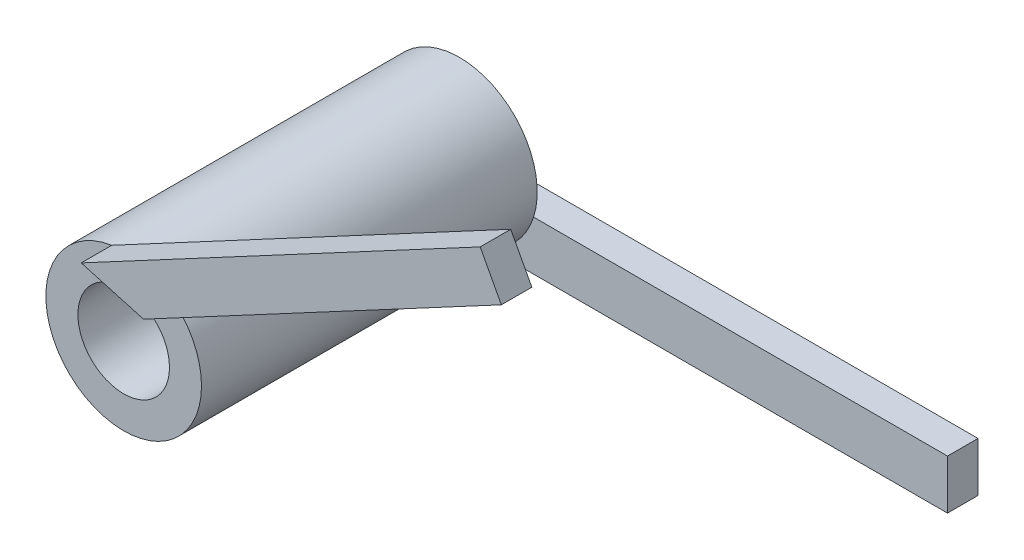
SolidWorks part; units mm, degrees
ref_plane "Front Plane" through (0, 0, 0) normal (0, 0, 1) x (1, 0, 0)
ref_plane "Top Plane" through (0, 0, 0) normal (0, 1, 0) x (1, 0, 0)
ref_plane "Right Plane" through (0, 0, 0) normal (1, 0, 0) x (0, 0, -1)
sketch "Sketch1" plane through (0, 0, 0) normal (0, 0, 1) x (1, 0, 0)
  circle A0 centre (0, 0) radius 2.55
  dimension "D1" = 5.1
extrude "Extrude1" add sketch "Sketch1" along normal blind 11
sketch "Sketch2" plane through (0, 0, 11) normal (0, 0, 1) x (1, 0, 0)
  line L0 (1.6509, 1.9435) -> (13.3744, 8.2127)
  line L1 (13.3744, 8.2127) -> (12.6807, 9.51)
  line L2 (12.6807, 9.51) -> (-0.3909, 2.5199)
  line L3 (-0.3909, 2.5199) -> (1.6509, 1.9435)
  circle A0 centre (0, 0) radius 2.55 construction
extrude "Extrude2" add sketch "Sketch2" along normal blind 1
sketch "Sketch3" plane through (0, 0, 0) normal (0, 0, -1) x (-1, 0, 0)
  line L0 (-0.8922, -2.3888) -> (-15.9921, -2.3888)
  line L1 (-15.9921, -2.3888) -> (-15.9921, -0.7692)
  line L2 (-15.9921, -0.7692) -> (-0.8922, -0.7692)
  line L3 (-0.8922, -0.7692) -> (-0.8922, -2.3888)
  circle A0 centre (0, 0) radius 2.55 construction
extrude "Extrude3" add sketch "Sketch3" along normal blind 1
sketch "Sketch4" plane through (0, 0, 11) normal (0, 0, 1) x (1, 0, 0)
  circle A0 centre (0, 0) radius 1.5
  dimension "D1" = 3
extrude "Extrude4" cut sketch "Sketch4" against normal through all
